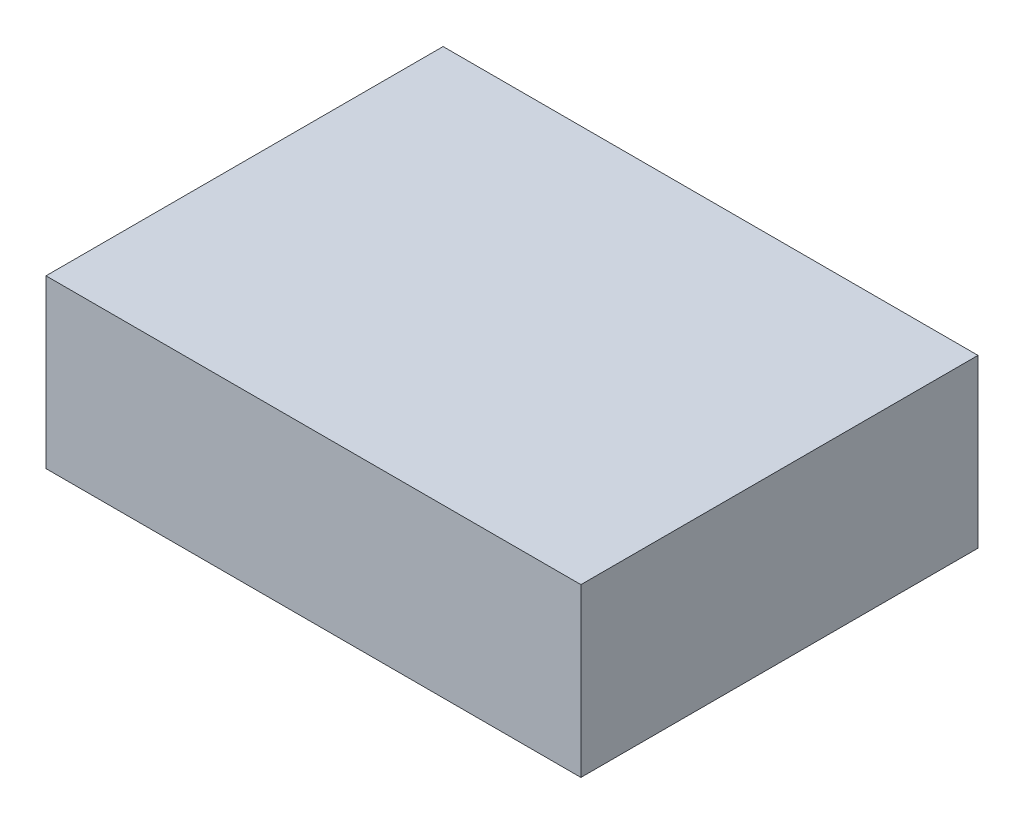
SolidWorks part; units mm, degrees
material "1.2343 (X38CrMoV5-1)"
ref_plane "Alzado" through (0, 0, 0) normal (0, 0, 1) x (1, 0, 0)
ref_plane "Planta" through (0, 0, 0) normal (0, 1, 0) x (1, 0, 0)
ref_plane "Vista lateral" through (0, 0, 0) normal (1, 0, 0) x (0, 0, -1)
sketch "Croquis1" plane through (0, 0, 0) normal (0, 1, 0) x (1, 0, 0)
  line L1 (-240.2236, -178.3337) -> (240.2236, -178.3337)
  line L2 (-240.2236, -178.3337) -> (-240.2236, 178.3337)
  line L3 (-240.2236, 178.3337) -> (240.2236, 178.3337)
  line L4 (240.2236, -178.3337) -> (240.2236, 178.3337)
  line L5 (-240.2236, -178.3337) -> (240.2236, 178.3337) construction
  line L6 (-240.2236, 178.3337) -> (240.2236, -178.3337) construction
  point P0 (0, 0)
  point P6 (233.7883, 113.0273)
  point P7 (240.2236, 178.3337)
extrude "Saliente-Extruir1" add sketch "Croquis1" along normal blind 150
